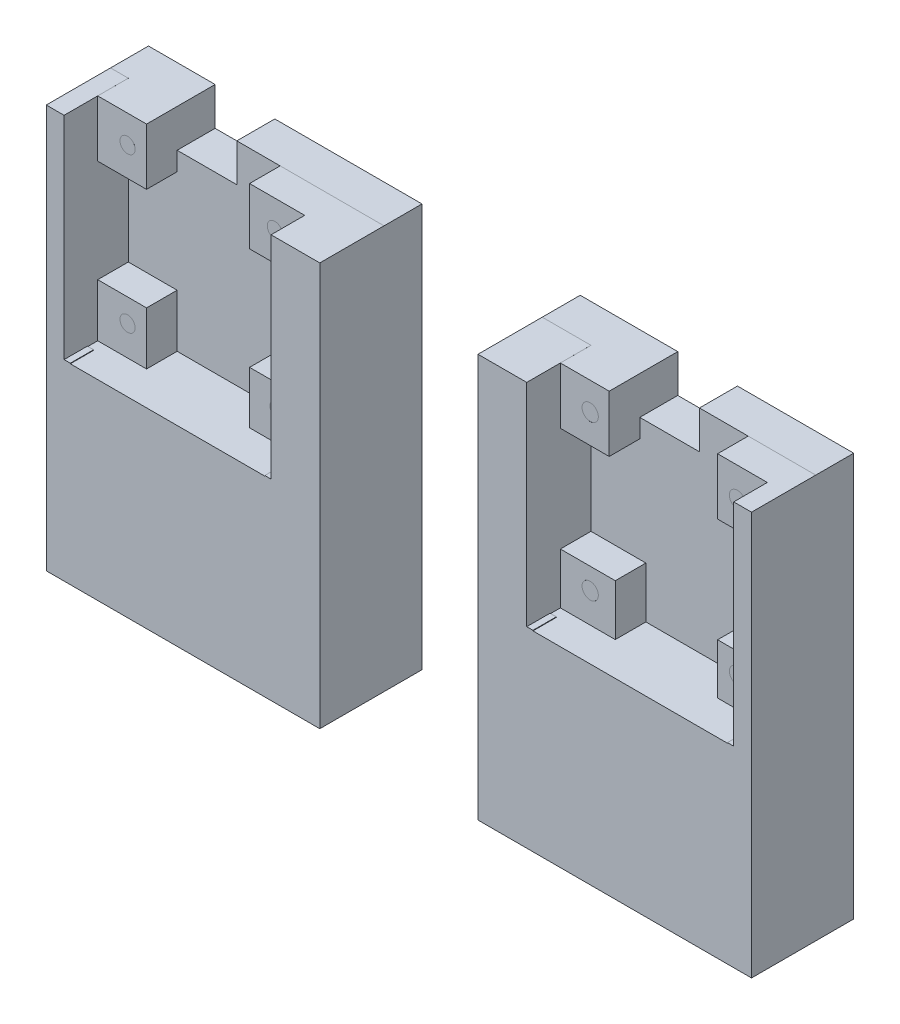
SolidWorks part; units mm, degrees
ref_plane "Front Plane" through (0, 0, 0) normal (0, 0, 1) x (1, 0, 0)
ref_plane "Top Plane" through (0, 0, 0) normal (0, 1, 0) x (1, 0, 0)
ref_plane "Right Plane" through (0, 0, 0) normal (1, 0, 0) x (0, 0, -1)
sketch "Sketch2" plane through (0, 0, 0) normal (0, 1, 0) x (1, 0, 0)
  line L1 (-65, -20) -> (65, -20)
  line L2 (-65, -20) -> (-65, 20)
  line L3 (-65, 20) -> (65, 20)
  line L4 (65, -20) -> (65, 20)
  line L5 (-65, -20) -> (65, 20) construction
  line L6 (-65, 20) -> (65, -20) construction
  point P0 (0, 0)
extrude "Boss-Extrude1" add sketch "Sketch2" along normal blind 75
sketch "Sketch5" plane through (0, 0, 20) normal (0, 0, 1) x (1, 0, 0)
  line L0 (-65, 75) -> (65, 75) construction
  line L1 (-65, 75) -> (-20.28, 75)
  line L2 (-65, 75) -> (-65, 50)
  line L3 (-65, 50) -> (-20.28, 50)
  line L4 (-20.28, 75) -> (-20.28, 50)
  line L6 (65, 75) -> (65, 50)
  line L7 (65, 50) -> (20.28, 50)
  line L8 (20.28, 75) -> (20.28, 50)
  line L9 (-14.58, 75) -> (14.58, 75)
  line L10 (-14.58, 75) -> (-14.58, 25.68)
  line L11 (-14.58, 25.68) -> (14.58, 25.68)
  line L12 (14.58, 75) -> (14.58, 25.68)
  point P10 (-20.28, 71.4)
  point P11 (0, 25.68)
  dimension "D1" = 44.72
  dimension "D2" = 25
  dimension "D3" = 25
  dimension "D4" = 44.72
  dimension "D5" = 21.4
  dimension "D6" = 45.72
  dimension "D7" = 29.16
  dimension "D8" = 5.7
  dimension "D9" = 5.7
sketch "Sketch6" plane through (0, 0, 20) normal (0, 0, 1) x (1, 0, 0)
  line L1 (-14.58, 75) -> (14.58, 75)
  line L2 (-14.58, 75) -> (-14.58, 25.68)
  line L3 (-14.58, 25.68) -> (14.58, 25.68)
  line L4 (14.58, 75) -> (14.58, 25.68)
extrude "Boss-Extrude2" add sketch "Sketch6" along normal blind 16.07
sketch "Sketch7" plane through (0, 0, 36.07) normal (0, 0, 1) x (1, 0, 0)
  line L0 (-14.58, 32.35) -> (14.58, 32.35)
  line L1 (-14.58, 75) -> (-14.58, 25.68) construction
  line L2 (14.58, 75) -> (14.58, 25.68) construction
  line L3 (-14.58, 25.68) -> (14.58, 25.68) construction
  line L4 (-7.98, 32.35) -> (-7.98, 75)
  line L5 (-14.58, 75) -> (14.58, 75) construction
  line L6 (7.98, 32.35) -> (7.98, 75)
  line L7 (-7.98, 75) -> (7.98, 75)
  line L9 (-7.98, 75) -> (7.98, 75)
  line L10 (-7.98, 75) -> (-7.98, 32.35)
  line L11 (-7.98, 32.35) -> (7.98, 32.35)
  line L12 (7.98, 75) -> (7.98, 32.35)
  line M8 (14.58, 75) -> (-14.58, 75)
  dimension "D1" = 6.67
  dimension "D2" = 6.6
  dimension "D3" = 6.6
extrude "Cut-Extrude1" cut sketch "Sketch7" against normal blind 8.48 contours L0 L6 L4 M8
sketch "Sketch8" plane through (-7.98, 0, 0) normal (1, 0, 0) x (0, 0, -1)
  line L0 (-27.59, 32.35) -> (-36.07, 32.35) construction
  line L1 (-27.59, 75) -> (-34.59, 75)
  line L2 (-27.59, 75) -> (-27.59, 32.35)
  line L3 (-27.59, 32.35) -> (-34.59, 32.35)
  line L4 (-34.59, 75) -> (-34.59, 32.35)
  dimension "D1" = 7
sketch "Sketch9" plane through (7.98, 0, 0) normal (-1, 0, 0) x (0, 0, 1)
  line L0 (27.59, 32.35) -> (36.07, 32.35) construction
  line L1 (27.59, 75) -> (34.59, 75)
  line L2 (27.59, 75) -> (27.59, 32.35)
  line L3 (27.59, 32.35) -> (34.59, 32.35)
  line L4 (34.59, 75) -> (34.59, 32.35)
  dimension "D1" = 7
extrude "Cut-Extrude2" cut sketch "Sketch8" against normal blind 1.145
extrude "Cut-Extrude3" cut sketch "Sketch9" against normal blind 1.145
sketch "Sketch11" plane through (0, 0, 20) normal (0, 0, 1) x (1, 0, 0)
  line L0 (20.28, 53.9) -> (65, 53.9)
  line L1 (20.28, 75) -> (65, 75)
  line L2 (20.28, 75) -> (20.28, 50)
  line L3 (20.28, 50) -> (65, 50)
  line L4 (65, 75) -> (65, 50)
  line L5 (24.71, 75) -> (24.71, 53.9)
  line L6 (60.57, 75) -> (60.57, 53.9)
  line L8 (24.71, 75) -> (60.57, 75)
  line L9 (24.71, 75) -> (24.71, 53.9)
  line L10 (24.71, 53.9) -> (60.57, 53.9)
  line L11 (60.57, 75) -> (60.57, 53.9)
  dimension "D1" = 3.9
  dimension "D2" = 4.43
  dimension "D3" = 4.43
extrude "Cut-Extrude4" cut sketch "Sketch11" against normal blind 8.2 contours L6 L1 L5 L0
sketch "Sketch13" plane through (24.71, 0, 0) normal (1, 0, 0) x (0, 0, -1)
  line L0 (-11.8, 53.9) -> (-20, 53.9) construction
  line L1 (-11.8, 75) -> (-15.7, 75)
  line L2 (-11.8, 75) -> (-11.8, 53.9)
  line L3 (-11.8, 53.9) -> (-15.7, 53.9)
  line L4 (-15.7, 75) -> (-15.7, 53.9)
  dimension "D1" = 3.9
sketch "Sketch14" plane through (60.57, 0, 0) normal (-1, 0, 0) x (0, 0, 1)
  line L0 (11.8, 53.9) -> (20, 53.9) construction
  line L1 (11.8, 75) -> (15.7, 75)
  line L2 (11.8, 75) -> (11.8, 53.9)
  line L3 (11.8, 53.9) -> (15.7, 53.9)
  line L4 (15.7, 75) -> (15.7, 53.9)
  dimension "D1" = 3.9
extrude "Cut-Extrude5" cut sketch "Sketch13" against normal blind 1.145
extrude "Cut-Extrude6" cut sketch "Sketch14" against normal blind 1.145
sketch "Sketch15" plane through (0, 0, 20) normal (0, 0, 1) x (1, 0, 0)
  line L0 (-65, 53.9) -> (-20.28, 53.9)
  line L1 (-65, 75) -> (-65, 50) construction
  line L2 (-20.28, 75) -> (-20.28, 50) construction
  line L3 (-65, 50) -> (-20.28, 50) construction
  line L4 (-60.57, 75) -> (-60.57, 53.9)
  line L5 (-65, 75) -> (-20.28, 75) construction
  line L6 (-24.71, 53.9) -> (-24.71, 75)
  line L7 (-60.57, 75) -> (-24.71, 75)
  line M11 (-14.58, 75) -> (-65, 75)
  dimension "D1" = 3.9
  dimension "D2" = 4.43
  dimension "D3" = 4.43
extrude "Cut-Extrude7" cut sketch "Sketch15" against normal blind 8.2 contours L0 L6 L4 M11
sketch "Sketch16" plane through (-60.57, 0, 0) normal (1, 0, 0) x (0, 0, -1)
  line L0 (-11.8, 53.9) -> (-20, 53.9) construction
  line L1 (-11.8, 75) -> (-15.7, 75)
  line L2 (-11.8, 75) -> (-11.8, 53.9)
  line L3 (-11.8, 53.9) -> (-15.7, 53.9)
  line L4 (-15.7, 75) -> (-15.7, 53.9)
  dimension "D1" = 3.9
extrude "Cut-Extrude8" cut sketch "Sketch16" against normal blind 1.145
sketch "Sketch17" plane through (-24.71, 0, 0) normal (-1, 0, 0) x (0, 0, 1)
  line L0 (11.8, 53.9) -> (20, 53.9) construction
  line L1 (11.8, 75) -> (15.7, 75)
  line L2 (11.8, 75) -> (11.8, 53.9)
  line L3 (11.8, 53.9) -> (15.7, 53.9)
  line L4 (15.7, 75) -> (15.7, 53.9)
  dimension "D1" = 3.9
extrude "Cut-Extrude9" cut sketch "Sketch17" against normal blind 1.145
sketch "Sketch20" plane through (0, 25.68, 0) normal (0, -1, 0) x (-1, 0, 0)
  line L1 (14.58, -36.07) -> (-14.58, -36.07)
  line L2 (14.58, -36.07) -> (14.58, -20)
  line L3 (14.58, -20) -> (-14.58, -20)
  line L4 (-14.58, -36.07) -> (-14.58, -20)
extrude "Boss-Extrude3" add sketch "Sketch20" along normal blind 25.68
sketch "Sketch21" plane through (0, 75, 0) normal (0, 1, 0) x (1, 0, 0)
  line L1 (65, 20) -> (25, 20)
  line L2 (65, 20) -> (65, -5)
  line L3 (65, -5) -> (25, -5)
  line L4 (25, 20) -> (25, -5)
  line L5 (-65, 20) -> (-25, 20)
  line L6 (-65, 20) -> (-65, -5)
  line L7 (-65, -5) -> (-25, -5)
  line L8 (-25, 20) -> (-25, -5)
  dimension "D1" = 25
  dimension "D2" = 40
  dimension "D3" = 40
extrude "Cut-Extrude10" cut sketch "Sketch21" against normal blind 40
sketch "Sketch22" plane through (0, 75, 0) normal (0, 1, 0) x (1, 0, 0)
  line L1 (-25, -5) -> (25, -5)
  line L2 (-25, -5) -> (-25, 20)
  line L3 (-25, 20) -> (25, 20)
  line L4 (25, -5) -> (25, 20)
extrude "Cut-Extrude11" cut sketch "Sketch22" against normal blind 40
sketch "Sketch23" plane through (0, 53.9, 0) normal (0, 1, 0) x (1, 0, 0)
  line L0 (-60.57, -20) -> (-60.57, -15.7)
  line L1 (-60.57, -15.7) -> (-61.715, -15.7)
  line L2 (-61.715, -15.7) -> (-61.715, -11.8)
  line L3 (-61.715, -11.8) -> (-23.565, -11.8)
  line L4 (-23.565, -11.8) -> (-23.565, -15.7)
  line L5 (-23.565, -15.7) -> (-24.71, -15.7)
  line L6 (-24.71, -15.7) -> (-24.71, -20)
  line L7 (-24.71, -20) -> (-60.57, -20)
extrude "Boss-Extrude4" add sketch "Sketch23" along normal blind 8
sketch "Sketch24" plane through (0, 53.9, 0) normal (0, 1, 0) x (1, 0, 0)
  line L0 (24.71, -20) -> (24.71, -15.7)
  line L1 (24.71, -15.7) -> (23.565, -15.7)
  line L2 (23.565, -15.7) -> (23.565, -11.8)
  line L3 (23.565, -11.8) -> (61.715, -11.8)
  line L4 (61.715, -11.8) -> (61.715, -15.7)
  line L5 (61.715, -15.7) -> (60.57, -15.7)
  line L6 (60.57, -15.7) -> (60.57, -20)
  line L7 (60.57, -20) -> (24.71, -20)
extrude "Boss-Extrude5" add sketch "Sketch24" along normal blind 8
sketch "Sketch25" plane through (0, 0, 36.07) normal (0, 0, 1) x (1, 0, 0)
  line L0 (-65, 75) -> (-65, 0) construction
  line L1 (-65, 26.6373) -> (65, 26.6373)
  line L2 (-65, 26.6373) -> (-65, 0)
  line L3 (-65, 0) -> (65, 0)
  line L4 (65, 26.6373) -> (65, 0)
extrude "Cut-Extrude12" cut sketch "Sketch25" against normal through all
sketch "Sketch26" plane through (0, 35, 0) normal (0, 1, 0) x (1, 0, 0)
  line L1 (-65, 20) -> (65, 20)
  line L2 (-65, 20) -> (-65, -5)
  line L3 (-65, -5) -> (65, -5)
  line L4 (65, 20) -> (65, -5)
extrude "Boss-Extrude6" add sketch "Sketch26" along normal up to vertex (40 mm away)
sketch "Sketch27" plane through (0, 0, 36.07) normal (0, 0, 1) x (1, 0, 0)
  line L1 (-14.58, 75) -> (14.58, 75)
  line L2 (-14.58, 75) -> (-14.58, 26.6373)
  line L3 (-14.58, 26.6373) -> (14.58, 26.6373)
  line L4 (14.58, 75) -> (14.58, 26.6373)
extrude "Cut-Extrude13" cut sketch "Sketch27" against normal through all
sketch "Sketch30" plane through (0, 75, 0) normal (0, 1, 0) x (1, 0, 0)
  line L0 (-65, 20) -> (-65, -20)
  line L1 (-65, -20) -> (-60.57, -20)
  line L2 (-60.57, -20) -> (-60.57, -15.7)
  line L3 (-60.57, -15.7) -> (-61.715, -15.7)
  line L4 (-61.715, -15.7) -> (-61.715, -11.8)
  line L5 (-61.715, -11.8) -> (-23.565, -11.8)
  line L6 (-23.565, -11.8) -> (-23.565, -15.7)
  line L7 (-23.565, -15.7) -> (-24.71, -15.7)
  line L8 (-24.71, -15.7) -> (-24.71, -20)
  line L9 (-24.71, -20) -> (-14.58, -20)
  line L10 (-14.58, -20) -> (-14.58, 20)
  line L11 (-14.58, 20) -> (-65, 20)
extrude "Boss-Extrude9" add sketch "Sketch30" along normal blind 26
sketch "Sketch31" plane through (0, 75, 0) normal (0, 1, 0) x (1, 0, 0)
  line L0 (14.58, 20) -> (14.58, -20)
  line L1 (14.58, -20) -> (24.71, -20)
  line L2 (24.71, -20) -> (24.71, -15.7)
  line L3 (24.71, -15.7) -> (23.565, -15.7)
  line L4 (23.565, -15.7) -> (23.565, -11.8)
  line L5 (23.565, -11.8) -> (61.715, -11.8)
  line L6 (61.715, -11.8) -> (61.715, -15.7)
  line L7 (61.715, -15.7) -> (60.57, -15.7)
  line L8 (60.57, -15.7) -> (60.57, -20)
  line L9 (60.57, -20) -> (65, -20)
  line L10 (65, -20) -> (65, 20)
  line L11 (65, 20) -> (14.58, 20)
extrude "Boss-Extrude10" add sketch "Sketch31" along normal blind 26
sketch "Sketch32" plane through (0, 0, 11.8) normal (0, 0, 1) x (1, 0, 0)
  line L0 (-61.715, 61.9) -> (-61.715, 101) construction
  line L2 (-23.565, 61.9) -> (-61.715, 61.9) construction
  line L3 (-23.565, 101) -> (-23.565, 61.9) construction
  line L4 (-23.565, 101) -> (-23.565, 61.9)
  line L5 (-23.565, 61.9) -> (-61.715, 61.9)
  line L6 (-61.715, 61.9) -> (-61.715, 101)
  line L7 (-61.715, 101) -> (-23.565, 101)
  circle A0 centre (-56.215, 95.9) radius 2.5
  circle A1 centre (-56.215, 67.4) radius 2.5
  circle A2 centre (-29.065, 95.8956) radius 2.5
  circle A3 centre (-28.565, 67.4) radius 2.5
  dimension "D1" = 5.5
  dimension "D3" = 5.5
  dimension "D5" = 5.5
  dimension "D6" = 28.5
  dimension "D2" = 28.5
  dimension "D4" = 5.5
  dimension "D7" = 5.5
extrude "Cut-Extrude14" cut sketch "Sketch32" against normal blind 24
sketch "Sketch33" plane through (0, 0, 11.8) normal (0, 0, 1) x (1, 0, 0)
  circle A0 centre (-56.215, 95.9) radius 1.4
  circle A1 centre (-56.215, 67.4) radius 1.4
  circle A2 centre (-29.065, 95.8956) radius 1.4
  circle A3 centre (-28.565, 67.4) radius 1.4
extrude "Boss-Extrude11" add sketch "Sketch33" along normal blind 2
sketch "Sketch34" plane through (0, 101, 0) normal (0, 1, 0) x (1, 0, 0)
  line L0 (-61.715, -15.7) -> (-61.715, -20)
  line L1 (-65, -20) -> (-60.57, -20) construction
  line L2 (-61.715, -20) -> (-60.57, -20)
  line L3 (-60.57, -20) -> (-60.57, -15.7)
  line L4 (-60.57, -15.7) -> (-61.715, -15.7)
  line L5 (-23.565, -15.7) -> (-23.565, -20)
  line L6 (-24.71, -20) -> (-14.58, -20) construction
  line L7 (-23.565, -20) -> (-24.71, -20)
  line L8 (-24.71, -20) -> (-24.71, -15.7)
  line L9 (-24.71, -15.7) -> (-23.565, -15.7)
extrude "Cut-Extrude15" cut sketch "Sketch34" against normal blind 39
sketch "Sketch35" plane through (0, 0, 11.8) normal (0, 0, 1) x (1, 0, 0)
  line L0 (61.715, 61.9) -> (23.565, 61.9) construction
  line L1 (23.565, 61.9) -> (23.565, 101) construction
  line L2 (61.715, 101) -> (61.715, 61.9) construction
  line L3 (23.565, 61.9) -> (23.565, 101)
  line L4 (23.565, 101) -> (61.715, 101)
  line L5 (61.715, 101) -> (61.715, 61.9)
  line L6 (61.715, 61.9) -> (23.565, 61.9)
  circle A0 centre (29.065, 67.4) radius 2.5
  circle A1 centre (29.065, 95.9) radius 2.5
  circle A2 centre (56.215, 67.4) radius 2.5
  circle A3 centre (56.215, 95.5) radius 2.5
  dimension "D1" = 5.5
  dimension "D5" = 5.5
  dimension "D2" = 5.5
  dimension "D3" = 5.5
  dimension "D4" = 28.5
  dimension "D6" = 5.5
  dimension "D7" = 5.5
  dimension "D8" = 5.5
extrude "Cut-Extrude16" cut sketch "Sketch35" against normal blind 24
sketch "Sketch36" plane through (0, 101, 0) normal (0, 1, 0) x (1, 0, 0)
  line L0 (23.565, -15.7) -> (23.565, -20)
  line L1 (14.58, -20) -> (24.71, -20) construction
  line L2 (23.565, -20) -> (24.71, -20)
  line L3 (24.71, -20) -> (24.71, -15.7)
  line L4 (24.71, -15.7) -> (23.565, -15.7)
  line L5 (60.57, -20) -> (60.57, -15.7)
  line L6 (60.57, -15.7) -> (61.715, -15.7)
  line L7 (61.715, -15.7) -> (61.715, -20)
  line L8 (60.57, -20) -> (65, -20) construction
  line L9 (61.715, -20) -> (60.57, -20)
extrude "Cut-Extrude17" cut sketch "Sketch36" against normal blind 39
sketch "Sketch37" plane through (0, 0, 11.8) normal (0, 0, 1) x (1, 0, 0)
  circle A0 centre (29.065, 95.9) radius 1.5
  circle A1 centre (29.065, 67.4) radius 1.5
  circle A2 centre (56.215, 95.5) radius 1.5
  circle A3 centre (56.215, 67.4) radius 1.5
extrude "Boss-Extrude12" add sketch "Sketch37" along normal blind 2
sketch "Sketch41" plane through (0, 0, -12.2) normal (0, 0, 1) x (1, 0, 0)
  line L0 (-23.565, 101) -> (-61.715, 101) construction
  line L2 (-51.715, 101) -> (-40.715, 101)
  line L3 (-51.715, 101) -> (-51.715, 95.5)
  line L4 (-51.715, 95.5) -> (-40.715, 95.5)
  line L5 (-40.715, 101) -> (-40.715, 95.5)
  point P0 (-51.715, 101)
  dimension "D1" = 10
  dimension "D2" = 11
  dimension "D3" = 5.5
extrude "Cut-Extrude18" cut sketch "Sketch41" against normal through all
sketch "Sketch42" plane through (0, 0, -12.2) normal (0, 0, 1) x (1, 0, 0)
  line L0 (61.715, 101) -> (23.565, 101) construction
  line L2 (33.565, 101) -> (44.565, 101)
  line L3 (33.565, 101) -> (33.565, 95.5)
  line L4 (33.565, 95.5) -> (44.565, 95.5)
  line L5 (44.565, 101) -> (44.565, 95.5)
  point P0 (33.565, 101)
  dimension "D1" = 10
  dimension "D2" = 11
  dimension "D3" = 5.5
extrude "Cut-Extrude19" cut sketch "Sketch42" against normal through all
sketch "Sketch43" plane through (0, 26.6373, 0) normal (0, -1, 0) x (-1, 0, 0)
  line L0 (65, -20) -> (14.58, -20) construction
  line L1 (65, 20) -> (65, -20) construction
  line L2 (14.58, 20) -> (65, 20) construction
  line L3 (14.58, 20) -> (14.58, -20) construction
  circle A0 centre (60, -15) radius 3
  circle A1 centre (60, 15) radius 3
  circle A2 centre (19.58, -15) radius 3
  circle A3 centre (19.58, 15) radius 3
  dimension "D1" = 5
  dimension "D2" = 5
  dimension "D3" = 5
  dimension "D4" = 5
  dimension "D5" = 5
  dimension "D6" = 5
  dimension "D7" = 5
  dimension "D8" = 5
extrude "Cut-Extrude20" cut sketch "Sketch43" against normal blind 10
sketch "Sketch44" plane through (0, 26.6373, 0) normal (0, -1, 0) x (1, 0, 0)
  line L0 (14.58, 20) -> (65, 20) construction
  line L1 (14.58, -20) -> (14.58, 20) construction
  line L2 (65, -20) -> (14.58, -20) construction
  line L3 (65, -20) -> (65, 20) construction
  circle A0 centre (19.58, 15) radius 3
  circle A1 centre (19.58, -15) radius 3
  circle A2 centre (60, 15) radius 3
  circle A3 centre (60, -15) radius 3
  dimension "D1" = 5
  dimension "D2" = 5
  dimension "D3" = 5
  dimension "D4" = 5
  dimension "D5" = 5
  dimension "D6" = 5
  dimension "D7" = 5
  dimension "D8" = 5
extrude "Cut-Extrude21" cut sketch "Sketch44" against normal blind 10
sketch "Sketch45" plane through (0, 101, 0) normal (0, 1, 0) x (1, 0, 0)
  line L0 (14.58, 20) -> (14.58, -20) construction
  line L1 (65, 20) -> (14.58, 20)
  line L2 (65, 20) -> (65, -8.1591)
  line L3 (65, -8.1591) -> (14.58, -8.1591)
  line L4 (14.58, 20) -> (14.58, -8.1591)
extrude "Cut-Extrude22" cut sketch "Sketch45" against normal blind 90
sketch "Sketch46" plane through (0, 101, 0) normal (0, 1, 0) x (1, 0, 0)
  line L0 (-14.58, -20) -> (-14.58, 20) construction
  line L1 (-65, 20) -> (-14.58, 20)
  line L2 (-65, 20) -> (-65, -8.1591)
  line L3 (-65, -8.1591) -> (-14.58, -8.1591)
  line L4 (-14.58, 20) -> (-14.58, -8.1591)
extrude "Cut-Extrude23" cut sketch "Sketch46" against normal blind 90
sketch "Sketch47" plane through (0, 0, 8.1591) normal (0, 0, -1) x (-1, 0, 0)
  line L0 (-14.58, 26.6373) -> (-14.58, 101) construction
  line L1 (-65, 26.6373) -> (-14.58, 26.6373)
  line L2 (-65, 26.6373) -> (-65, 33.6373)
  line L3 (-65, 33.6373) -> (-14.58, 33.6373)
  line L4 (-14.58, 26.6373) -> (-14.58, 33.6373)
  line L5 (65, 26.6373) -> (65, 101) construction
  line L6 (14.58, 26.6373) -> (65, 26.6373)
  line L7 (14.58, 26.6373) -> (14.58, 33.6373)
  line L8 (14.58, 33.6373) -> (65, 33.6373)
  line L9 (65, 26.6373) -> (65, 33.6373)
  dimension "D1" = 7
extrude "Boss-Extrude13" add sketch "Sketch47" along normal blind 7
sketch "Sketch48" plane through (0, 33.6373, 0) normal (0, 1, 0) x (1, 0, 0)
  line L1 (65, -8.1591) -> (14.58, -8.1591)
  line L2 (65, -8.1591) -> (65, -1.1591)
  line L3 (65, -1.1591) -> (14.58, -1.1591)
  line L4 (14.58, -8.1591) -> (14.58, -1.1591)
  line L5 (-14.58, -8.1591) -> (-65, -8.1591)
  line L6 (-14.58, -8.1591) -> (-14.58, -1.1591)
  line L7 (-14.58, -1.1591) -> (-65, -1.1591)
  line L8 (-65, -8.1591) -> (-65, -1.1591)
extrude "Boss-Extrude14" add sketch "Sketch48" along normal blind 67.36
sketch "Sketch49" plane through (0, 0, 8.1591) normal (0, 0, 1) x (1, 0, 0)
  line L0 (-61.715, 100.9973) -> (-23.565, 100.9973) construction
  line L1 (-52.715, 100.9973) -> (-41.715, 100.9973)
  line L2 (-52.715, 100.9973) -> (-52.715, 93.9973)
  line L3 (-52.715, 93.9973) -> (-41.715, 93.9973)
  line L4 (-41.715, 100.9973) -> (-41.715, 93.9973)
  line L5 (23.565, 100.9973) -> (61.715, 100.9973) construction
  line L6 (32.565, 100.9973) -> (43.565, 100.9973)
  line L7 (32.565, 100.9973) -> (32.565, 93.9973)
  line L8 (32.565, 93.9973) -> (43.565, 93.9973)
  line L9 (43.565, 100.9973) -> (43.565, 93.9973)
  dimension "D1" = 9
  dimension "D2" = 11
  dimension "D3" = 11
  dimension "D4" = 7
  dimension "D5" = 7
  dimension "D6" = 9
extrude "Cut-Extrude24" cut sketch "Sketch49" against normal through all
sketch "Sketch50" plane through (0, 0, 8.1591) normal (0, 0, 1) x (1, 0, 0)
  line L0 (-61.715, 61.9) -> (-61.715, 100.9973) construction
  line L1 (-52.715, 100.9973) -> (-61.715, 100.9973)
  line L2 (-52.715, 100.9973) -> (-52.715, 90.572)
  line L3 (-52.715, 90.572) -> (-61.715, 90.572)
  line L4 (-61.715, 100.9973) -> (-61.715, 90.572)
  line L5 (-23.565, 61.9) -> (-61.715, 61.9) construction
  line L6 (-52.715, 61.9) -> (-61.715, 61.9)
  line L7 (-52.715, 61.9) -> (-52.715, 71.656)
  line L8 (-52.715, 71.656) -> (-61.715, 71.656)
  line L9 (-61.715, 61.9) -> (-61.715, 71.656)
  line L10 (-61.715, 62) -> (-61.715, 101) construction
  line L12 (-23.565, 62) -> (-33.7263, 62)
  line L13 (-23.565, 62) -> (-23.565, 71.656)
  line L14 (-23.565, 71.656) -> (-33.7263, 71.656)
  line L15 (-33.7263, 62) -> (-33.7263, 71.656)
  line L16 (-23.565, 101) -> (-33.7263, 101)
  line L17 (-23.565, 101) -> (-23.565, 90.572)
  line L18 (-23.565, 90.572) -> (-33.7263, 90.572)
  line L19 (-33.7263, 101) -> (-33.7263, 90.572)
extrude "Boss-Extrude15" add sketch "Sketch50" along normal blind 5.64
sketch "Sketch51" plane through (0, 0, 8.1591) normal (0, 0, 1) x (1, 0, 0)
  line L0 (23.565, 61.9) -> (23.565, 100.9973) construction
  line L1 (32.565, 100.9973) -> (23.565, 100.9973)
  line L2 (32.565, 100.9973) -> (32.565, 90.572)
  line L3 (32.565, 90.572) -> (23.565, 90.572)
  line L4 (23.565, 100.9973) -> (23.565, 90.572)
  line L6 (61.715, 101) -> (52.5473, 101)
  line L7 (61.715, 101) -> (61.715, 90.572)
  line L8 (61.715, 90.572) -> (52.5473, 90.572)
  line L9 (52.5473, 101) -> (52.5473, 90.572)
  line L10 (23.565, 61.9) -> (33.6841, 61.9)
  line L11 (23.565, 61.9) -> (23.565, 71.304)
  line L12 (23.565, 71.304) -> (33.6841, 71.304)
  line L13 (33.6841, 61.9) -> (33.6841, 71.304)
  line L15 (61.715, 62) -> (52.5473, 62)
  line L16 (61.715, 62) -> (61.715, 71.304)
  line L17 (61.715, 71.304) -> (52.5473, 71.304)
  line L18 (52.5473, 62) -> (52.5473, 71.304)
extrude "Boss-Extrude16" add sketch "Sketch51" along normal blind 5.64
